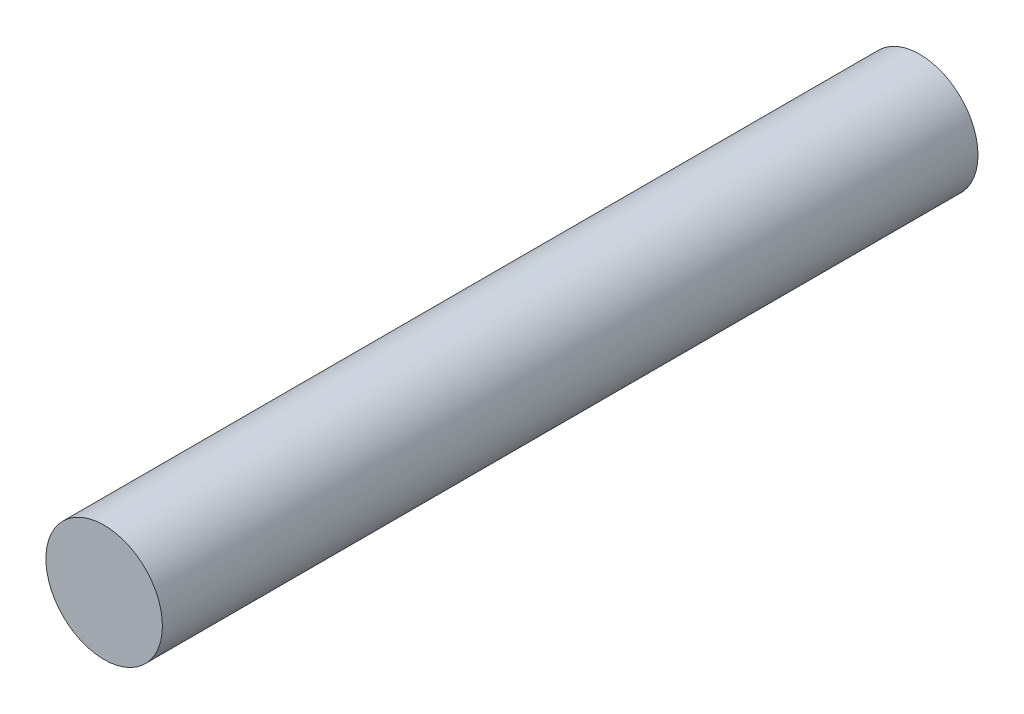
SolidWorks part; units mm, degrees
ref_plane "Front Plane" through (0, 0, 0) normal (0, 0, 1) x (1, 0, 0)
ref_plane "Top Plane" through (0, 0, 0) normal (0, 1, 0) x (1, 0, 0)
ref_plane "Right Plane" through (0, 0, 0) normal (1, 0, 0) x (0, 0, -1)
sketch "Sketch1" plane through (0, 0, 0) normal (0, 0, 1) x (1, 0, 0)
  circle A0 centre (0, 0) radius 1
  dimension "D1" = 2
extrude "Boss-Extrude1" add sketch "Sketch1" along normal blind 14
ref_plane "Plane1" through (0, 0, 7) normal (0, 0, 1) x (1, 0, 0)
